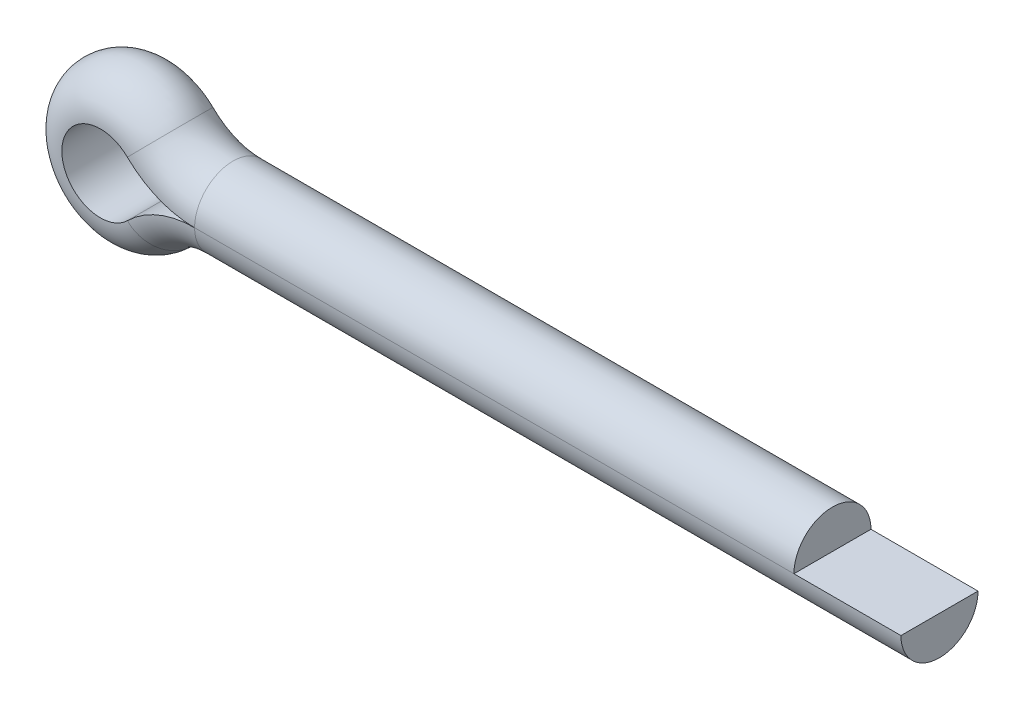
SolidWorks part; units mm, degrees
ref_plane "Front" through (0, 0, 0) normal (0, 0, 1) x (1, 0, 0)
ref_plane "Top" through (0, 0, 0) normal (0, 1, 0) x (1, 0, 0)
ref_plane "Right" through (0, 0, 0) normal (1, 0, 0) x (0, 0, -1)
ref_plane "Plane1" through (18, 0, 0) normal (1, 0, 0) x (0, 0, -1)
sketch "PathSke" plane through (1.208, 1.808, 0) normal (0, 0, 1) x (0, 1, 0)
  line L0 (-0.908, -16.792) -> (-0.908, -2.792)
  line L1 (-2.708, -2.792) -> (-2.708, -19.292)
  line L2 (-1.808, 1.208) -> (-1.808, -5.7761) construction
  arc A0 (-2.708, -2.792) -> (-3.0919, -1.8536) centre (-4.0469, -2.792) ccw
  arc A1 (-0.908, -2.792) -> (-0.5241, -1.8536) centre (0.4309, -2.792) cw
  arc A3 (-0.5241, -1.8536) -> (-3.0919, -1.8536) centre (-1.808, -0.592) ccw
  dimension "C" = 3.6
  dimension "d" = 1.8
  dimension "d/2" = 0.9
  dimension "l" = 14
  dimension "a" = 2.5
  dimension "b" = 4
sketch "SectionSke" plane through (18, 0.15, 0.15) normal (1, 0, 0) x (0, 1, 0)
  line L0 (-0.15, -1.05) -> (-0.15, 0.75)
  arc A0 (-0.15, -1.05) -> (-0.15, 0.75) centre (-0.15, -0.15) ccw
  dimension "R" = 0.9
  dimension "d1" = 1.8
sweep "Body" add profiles "SectionSke" path "PathSke"
equation "\"d/2@PathSke\" = \"d@PathSke\" / 2"
equation "\"R@SectionSke\" = \"d@PathSke\" / 2"
equation "\"d1@SectionSke\" = \"d@PathSke\""
equation "\"D1@Plane1\" = \"b@PathSke\" + \"l@PathSke\""
